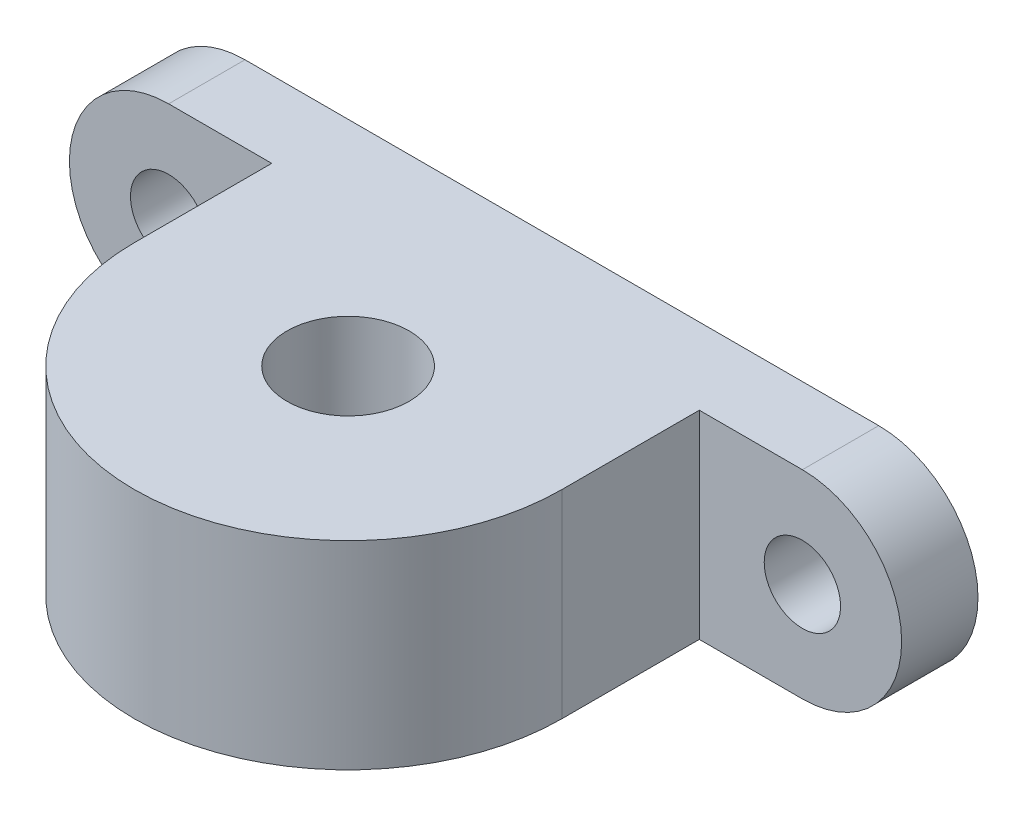
SolidWorks part; units mm, degrees
ref_plane "前视基准面" through (0, 0, 0) normal (0, 0, 1) x (1, 0, 0)
ref_plane "上视基准面" through (0, 0, 0) normal (0, 1, 0) x (1, 0, 0)
ref_plane "右视基准面" through (0, 0, 0) normal (1, 0, 0) x (0, 0, -1)
sketch "草图1" plane through (0, 0, 0) normal (0, 0, 1) x (1, 0, 0)
  line L0 (-20.75, -6.5) -> (20.75, -6.5)
  line L2 (-20.75, 6.5) -> (20.75, 6.5)
  line L3 (0, 0) -> (0, 11.9588) construction
  line L4 (-7.8065, 0) -> (-24.1828, 0) construction
  arc A0 (-20.75, 6.5) -> (-20.75, -6.5) centre (-20.75, 0) ccw
  arc A1 (20.75, 6.5) -> (20.75, -6.5) centre (20.75, 0) cw
  circle A2 centre (-20.75, 0) radius 2.5
  circle A3 centre (20.75, 0) radius 2.5
  point P12 (0, 6.5)
  dimension "D3" = 6.5
  dimension "D4" = 5
  dimension "D1" = 6.5
  dimension "D2" = 20.75
extrude "凸台-拉伸1" add sketch "草图1" along normal blind 5
sketch "草图2" plane through (0, -6.5, 0) normal (0, -1, 0) x (1, 0, 0)
  line L0 (-14, 14) -> (-14, 5)
  line L2 (0, 0) -> (0, 14) construction
  line L3 (-20.75, 0) -> (20.75, 0) construction
  line L4 (-20.75, 5) -> (20.75, 5) construction
  line L5 (14, 14) -> (14, 5)
  line L6 (14, 5) -> (-14, 5)
  arc A0 (14, 14) -> (-14, 14) centre (0, 14) ccw
  circle A1 centre (0, 14) radius 4
  dimension "D2" = 14
  dimension "D3" = 8
  dimension "D1" = 14
extrude "凸台-拉伸2" add sketch "草图2" against normal up to surface (13 mm away) up to face at (0, 6.5, 2.5)
